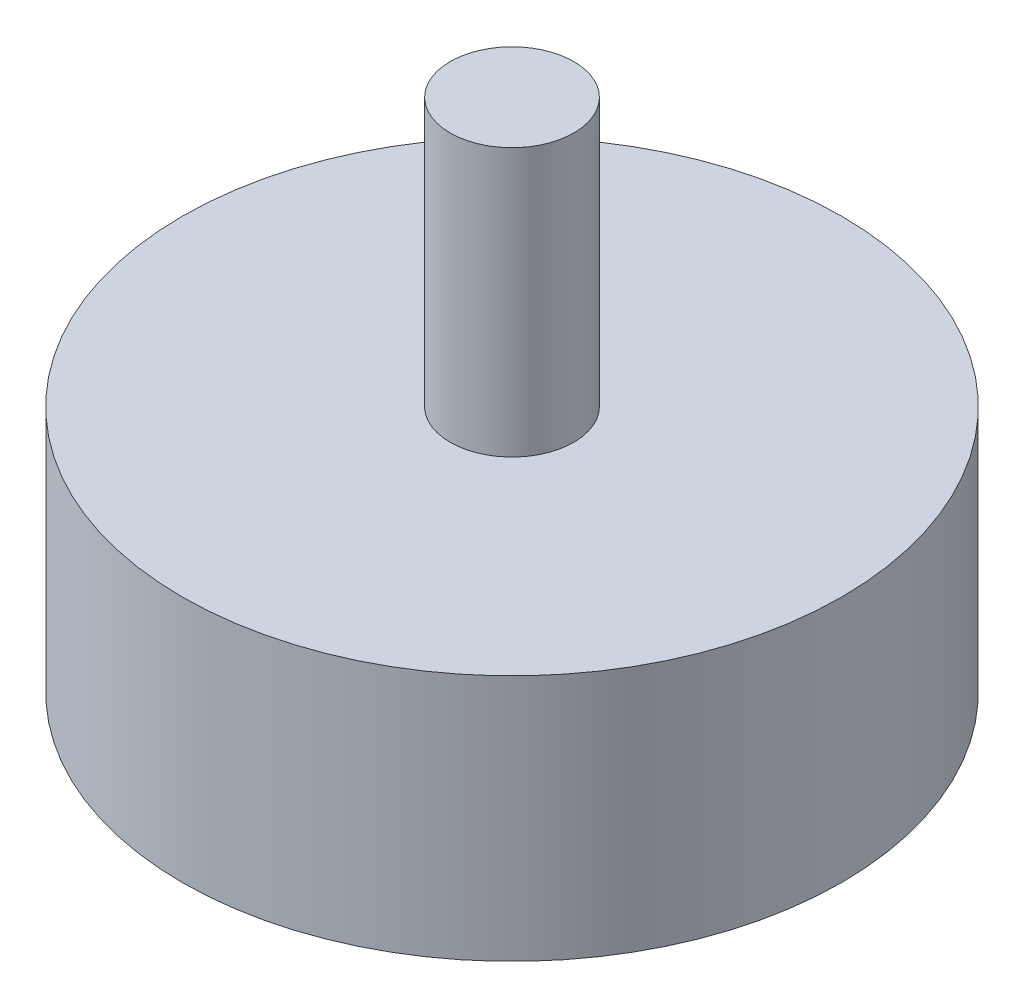
SolidWorks part; units mm, degrees
material "Rubber"
ref_plane "Front Plane" through (0, 0, 0) normal (0, 0, 1) x (1, 0, 0)
ref_plane "Top Plane" through (0, 0, 0) normal (0, 1, 0) x (1, 0, 0)
ref_plane "Right Plane" through (0, 0, 0) normal (1, 0, 0) x (0, 0, -1)
sketch "Sketch1" plane through (0, 0, 0) normal (0, 1, 0) x (1, 0, 0)
  circle A0 centre (0, 0) radius 25.4
  dimension "D1" = 50.8
extrude "Boss-Extrude1" add sketch "Sketch1" along normal mid plane 19.05
sketch "Sketch2" plane through (0, 9.525, 0) normal (0, 1, 0) x (1, 0, 0)
  circle A0 centre (0, 0) radius 4.7625
extrude "Boss-Extrude2" add sketch "Sketch2" along normal blind 20.6375
mirror "Mirror1" about plane through (0, 0, 0) normal (0, 1, 0) of "Boss-Extrude2"
sketch "Sketch3" plane through (0, -30.1625, 0) normal (0, -1, 0) x (-1, 0, 0)
  circle A0 centre (0, 0) radius 4.7625
extrude "Cut-Extrude1" cut sketch "Sketch3" against normal blind 7.9375
